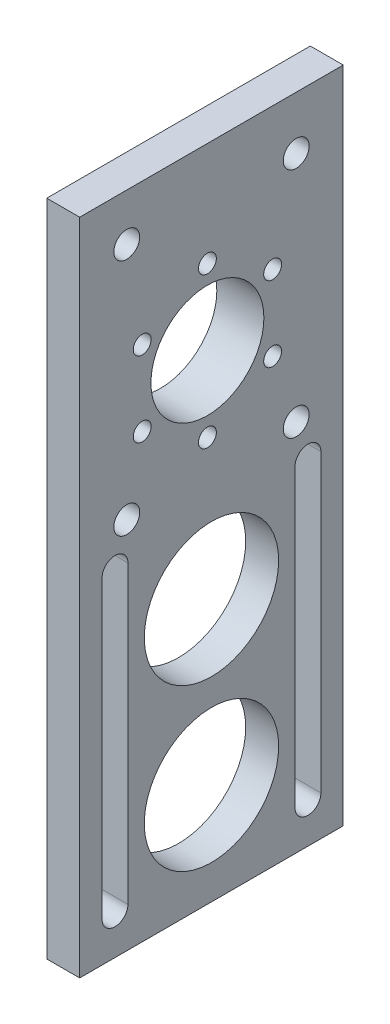
SolidWorks part; units mm, degrees
ref_plane "Front Plane" through (0, 0, 0) normal (0, 0, 1) x (1, 0, 0)
ref_plane "Top Plane" through (0, 0, 0) normal (0, 1, 0) x (1, 0, 0)
ref_plane "Right Plane" through (0, 0, 0) normal (1, 0, 0) x (0, 0, -1)
sketch "Sketch1" plane through (0, 0, 0) normal (1, 0, 0) x (0, 0, -1)
  line L1 (0, 0) -> (56, 0)
  line L2 (0, 0) -> (0, 140)
  line L3 (0, 140) -> (56, 140)
  line L4 (56, 0) -> (56, 140)
  dimension "D1" = 56
  dimension "D2" = 140
extrude "Boss-Extrude1" add sketch "Sketch1" along normal blind 7
sketch "Sketch2" plane through (7, 0, 0) normal (1, 0, 0) x (0, 0, -1)
  line L0 (0, 0) -> (56, 0) construction
  line L1 (28, 0) -> (28, 140) construction
  line L2 (56, 140) -> (0, 140) construction
  circle A0 centre (28, 21.5163) radius 14.275
  circle A1 centre (28, 55.7276) radius 14.275
  circle A3 centre (27.1376, 101.9141) radius 12 construction
  circle A4 centre (27.1376, 101.9141) radius 12
  circle A5 centre (13.2812, 109.9141) radius 1.25 construction
  circle A6 centre (13.2812, 109.9141) radius 1.25 construction
  circle A7 centre (27.1376, 117.9141) radius 1.25 construction
  circle A8 centre (27.1376, 117.9141) radius 1.25 construction
  circle A9 centre (27.1376, 85.9141) radius 1.25 construction
  circle A10 centre (27.1376, 85.9141) radius 1.25 construction
  circle A11 centre (40.994, 93.9141) radius 1.25 construction
  circle A12 centre (40.994, 93.9141) radius 1.25 construction
  circle A13 centre (13.2812, 93.9141) radius 1.25 construction
  circle A14 centre (13.2812, 93.9141) radius 1.25 construction
  circle A15 centre (13.2812, 109.9141) radius 1.25 construction
  circle A16 centre (40.994, 109.9141) radius 1.25 construction
  circle A17 centre (40.994, 109.9141) radius 1.25 construction
  circle A18 centre (40.994, 109.9141) radius 1.9
  circle A19 centre (27.1376, 117.9141) radius 1.9
  circle A20 centre (13.2812, 109.9141) radius 1.9
  circle A21 centre (40.994, 93.9141) radius 1.9
  circle A22 centre (27.1376, 85.9141) radius 1.9
  circle A23 centre (13.2812, 93.9141) radius 1.9
  point P5 (28, 0)
  dimension "D1" = 28.55
  dimension "D2" = 3.8
  dimension "D3" = 3.8
  dimension "D4" = 3.8
  dimension "D5" = 3.8
  dimension "D6" = 3.8
  dimension "D7" = 3.8
extrude "Cut-Extrude1" cut sketch "Sketch2" against normal through all
sketch "Sketch3" plane through (7, 0, 0) normal (1, 0, 0) x (0, 0, -1)
  line L0 (7.5, 71.2448) -> (7.5, 8.435) construction
  line L1 (10.25, 71.2448) -> (10.25, 8.435)
  line L2 (4.75, 71.2448) -> (4.75, 8.435)
  line L3 (48.5, 8.435) -> (48.5, 71.2448) construction
  line L4 (45.75, 8.435) -> (45.75, 71.2448)
  line L5 (51.25, 8.435) -> (51.25, 71.2448)
  line L6 (0, 140) -> (0, 0) construction
  line L7 (56, 0) -> (56, 140) construction
  arc A0 (10.25, 71.2448) -> (4.75, 71.2448) centre (7.5, 71.2448) ccw
  arc A1 (4.75, 8.435) -> (10.25, 8.435) centre (7.5, 8.435) ccw
  arc A2 (45.75, 8.435) -> (51.25, 8.435) centre (48.5, 8.435) ccw
  arc A3 (51.25, 71.2448) -> (45.75, 71.2448) centre (48.5, 71.2448) ccw
  point P2 (7.5, 39.8399)
  point P7 (48.5, 39.8399)
  dimension "D1" = 2.75
  dimension "D2" = 2.75
  dimension "D3" = 7.5
  dimension "D4" = 7.5
extrude "Cut-Extrude2" cut sketch "Sketch3" against normal through all
sketch "Sketch4" plane through (7, 0, 0) normal (1, 0, 0) x (0, 0, -1)
  line L0 (56, 0) -> (56, 140) construction
  line L1 (0, 140) -> (0, 0) construction
  line L2 (56, 140) -> (0, 140) construction
  circle A0 centre (10, 130) radius 2.75
  circle A1 centre (46, 128.7418) radius 2.75
  circle A2 centre (46, 79.3508) radius 2.75
  circle A3 centre (10, 79.3508) radius 2.75
  dimension "D1" = 5.5
  dimension "D2" = 5.5
  dimension "D9" = 5.5
  dimension "D10" = 5.5
  dimension "D3" = 10
  dimension "D4" = 10
  dimension "D5" = 10
  dimension "D6" = 11.2582
  dimension "D7" = 10
  dimension "D8" = 10
extrude "Cut-Extrude3" cut sketch "Sketch4" against normal through all
sketch "Sketch7" plane through (0, 0, 0) normal (-1, 0, 0) x (0, 0, 1)
  line L1 (-10.6436, 111.1546) -> (-26.8931, 120.8186)
  line L2 (-26.8931, 120.8186) -> (-43.3872, 111.5781)
  line L3 (-43.3872, 111.5781) -> (-43.6316, 92.6736)
  line L4 (-43.6316, 92.6736) -> (-27.3821, 83.0096)
  line L5 (-27.3821, 83.0096) -> (-10.8881, 92.2501)
  line L6 (-10.8881, 92.2501) -> (-10.6436, 111.1546)
  circle A0 centre (-27.1376, 101.9141) radius 16.3731 construction
extrude "Boss-Extrude3" add sketch "Sketch7" along normal blind 3
sketch "Sketch8" plane through (0, 0, 0) normal (1, 0, 0) x (0, 0, -1)
  circle A0 centre (13.2812, 109.9141) radius 1.9 construction
  circle A1 centre (13.2812, 93.9141) radius 1.9 construction
  circle A2 centre (27.1376, 85.9141) radius 1.9 construction
  circle A3 centre (40.994, 93.9141) radius 1.9 construction
  circle A4 centre (40.994, 109.9141) radius 1.9 construction
  circle A5 centre (27.1376, 117.9141) radius 1.9 construction
  circle A6 centre (27.1376, 101.9141) radius 12 construction
  circle A7 centre (13.2812, 109.9141) radius 1.9
  circle A8 centre (13.2812, 93.9141) radius 1.9
  circle A9 centre (27.1376, 85.9141) radius 1.9
  circle A10 centre (40.994, 93.9141) radius 1.9
  circle A11 centre (40.994, 109.9141) radius 1.9
  circle A12 centre (27.1376, 117.9141) radius 1.9
  circle A13 centre (27.1376, 101.9141) radius 12
extrude "Cut-Extrude5" cut sketch "Sketch8" against normal through all
